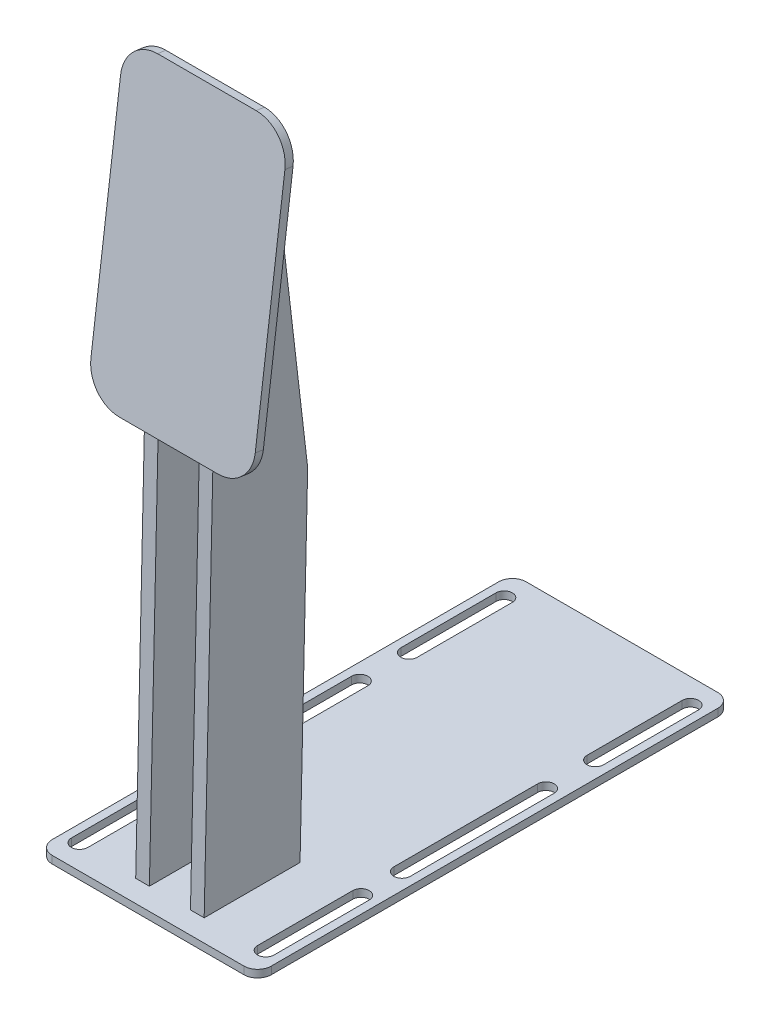
SolidWorks part; units mm, degrees
ref_plane "Front Plane" through (0, 0, 0) normal (0, 0, 1) x (1, 0, 0)
ref_plane "Top Plane" through (0, 0, 0) normal (0, 1, 0) x (1, 0, 0)
ref_plane "Right Plane" through (0, 0, 0) normal (1, 0, 0) x (0, 0, -1)
sketch "Sketch1" plane through (0, 0, 0) normal (0, 1, 0) x (1, 0, 0)
  line L0 (34, 77.5187) -> (34, 42.7687) construction
  line L1 (-35, 86.5188) -> (35, 86.5188)
  line L2 (-40, 81.5187) -> (-40, -81.5187)
  line L3 (-35, -86.5187) -> (35, -86.5187)
  line L4 (40, 81.5187) -> (40, -81.5187)
  line L5 (-40, 86.5188) -> (40, -86.5187) construction
  line L6 (-40, -86.5187) -> (40, 86.5188) construction
  line L7 (37, 77.5187) -> (37, 42.7687)
  line L8 (31, 77.5187) -> (31, 42.7687)
  line L9 (-40, 0) -> (40, 0) construction
  line L10 (0, 86.5188) -> (0, -86.5187) construction
  line L11 (-34, 77.5187) -> (-34, 42.7687) construction
  line L12 (-37, 77.5187) -> (-37, 42.7687)
  line L13 (-31, 77.5187) -> (-31, 42.7687)
  line L14 (34, -77.5187) -> (34, -42.7687) construction
  line L15 (37, -77.5187) -> (37, -42.7687)
  line L16 (31, -77.5187) -> (31, -42.7687)
  line L17 (-34, -77.5187) -> (-34, -42.7687) construction
  line L18 (-37, -77.5187) -> (-37, -42.7687)
  line L19 (-31, -77.5187) -> (-31, -42.7687)
  line L20 (34, 24.7687) -> (34, -27.7687) construction
  line L21 (37, 24.7687) -> (37, -27.7687)
  line L22 (31, 24.7687) -> (31, -27.7687)
  line L23 (-34, 24.7687) -> (-34, -27.7687) construction
  line L24 (-37, 24.7687) -> (-37, -27.7687)
  line L25 (-31, 24.7687) -> (-31, -27.7687)
  arc A0 (-40, -81.5187) -> (-35, -86.5187) centre (-35, -81.5187) ccw
  arc A1 (35, -86.5187) -> (40, -81.5187) centre (35, -81.5187) ccw
  arc A2 (35, 86.5188) -> (40, 81.5187) centre (35, 81.5187) cw
  arc A3 (-35, 86.5188) -> (-40, 81.5187) centre (-35, 81.5187) ccw
  arc A4 (37, 77.5187) -> (31, 77.5187) centre (34, 77.5187) ccw
  arc A5 (31, 42.7687) -> (37, 42.7687) centre (34, 42.7687) ccw
  arc A6 (-37, 77.5187) -> (-31, 77.5187) centre (-34, 77.5187) cw
  arc A7 (-31, 42.7687) -> (-37, 42.7687) centre (-34, 42.7687) cw
  arc A8 (37, -77.5187) -> (31, -77.5187) centre (34, -77.5187) cw
  arc A9 (31, -42.7687) -> (37, -42.7687) centre (34, -42.7687) cw
  arc A10 (-37, -77.5187) -> (-31, -77.5187) centre (-34, -77.5187) ccw
  arc A11 (-31, -42.7687) -> (-37, -42.7687) centre (-34, -42.7687) ccw
  arc A12 (37, 24.7687) -> (31, 24.7687) centre (34, 24.7687) ccw
  arc A13 (31, -27.7687) -> (37, -27.7687) centre (34, -27.7687) ccw
  arc A14 (-37, 24.7687) -> (-31, 24.7687) centre (-34, 24.7687) cw
  arc A15 (-31, -27.7687) -> (-37, -27.7687) centre (-34, -27.7687) cw
  circle A16 centre (0, -48.9201) radius 7.112
  point P0 (0, 0)
  point P20 (34, 60.1437)
  point P31 (-34, 60.1437)
  point P38 (34, -60.1437)
  point P45 (-34, -60.1437)
  point P52 (34, -1.5)
  point P59 (-34, -1.5)
  dimension "D3" = 5
  dimension "D6" = 6
  dimension "D5" = 40.75
  dimension "D9" = 12
  dimension "D10" = 9
  dimension "D1" = 80
  dimension "D2" = 173.0375
  dimension "D4" = 3
  dimension "D7" = 6
  dimension "D8" = 6
extrude "Boss-Extrude1" add sketch "Sketch1" along normal blind 2.75
sketch "Sketch2" plane through (0, 0, 0) normal (1, 0, 0) x (0, 0, -1)
  line L0 (-65.0187, 254) -> (-78.9187, 146)
  line L1 (-86.5187, 89.4829) -> (-86.5187, 186.7974) construction
  line L2 (-81.5187, 0) -> (81.5187, 0) construction
  dimension "D1" = 7.6
  dimension "D2" = 21.5
  dimension "D3" = 146
  dimension "D4" = 254
  dimension "D5" = 82.666
ref_plane "Plane1" through (0, 12.3707, 96.1173) normal (0, 0.1277, 0.9918) x (0, -0.9918, 0.1277)
sketch "Sketch3" plane through (0, 12.3707, 96.1173) normal (0, 0.1277, 0.9918) x (0, -0.9918, 0.1277)
  line L0 (-243.6224, 0) -> (-134.7316, 0) construction
  line L1 (-231.6224, 30) -> (-146.7316, 30)
  line L2 (-243.6224, 18) -> (-243.6224, -18)
  line L3 (-231.6224, -30) -> (-146.7316, -30)
  line L4 (-134.7316, 18) -> (-134.7316, -18)
  line L5 (-243.6224, 0) -> (-134.7316, 0) construction
  arc A0 (-231.6224, 30) -> (-243.6224, 18) centre (-231.6224, 18) ccw
  arc A1 (-243.6224, -18) -> (-231.6224, -30) centre (-231.6224, -18) ccw
  arc A2 (-146.7316, -30) -> (-134.7316, -18) centre (-146.7316, -18) ccw
  arc A3 (-146.7316, 30) -> (-134.7316, 18) centre (-146.7316, 18) cw
  point P6 (-243.6224, 0)
  point P7 (-134.7316, 0)
  dimension "D2" = 12
  dimension "D1" = 60
extrude "Boss-Extrude2" add sketch "Sketch3" against normal blind 3 separate body
ref_plane "Plane2" through (10, 0, 0) normal (1, 0, 0) x (0, 0, -1)
sketch "Sketch4" plane through (10, 0, 0) normal (1, 0, 0) x (0, 0, -1)
  line L0 (-75.1774, 151.568) -> (-78.5308, 2.75)
  line L1 (-75.9433, 145.617) -> (-74.4115, 157.5189) construction
  line L2 (-81.5187, 2.75) -> (81.5187, 2.75) construction
  line L3 (-78.5308, 2.75) -> (-43.5219, 2.75)
  line L4 (-43.5219, 2.75) -> (-40.7383, 126.2808)
  line L5 (-40.7383, 126.2808) -> (-54.3983, 243.089)
  line L6 (-54.3983, 243.089) -> (-63.3983, 243.089)
  line L7 (-63.5751, 241.7152) -> (-62.0433, 253.617) construction
  line L8 (-63.3983, 243.089) -> (-75.1774, 151.568)
  point P9 (-43.5219, 2.75)
  dimension "D1" = 9
  dimension "D2" = 35
extrude "Boss-Extrude3" add sketch "Sketch4" along normal mid plane 5
mirror "Mirror2" about plane through (0, 0, 0) normal (1, 0, 0) of "Boss-Extrude3"
